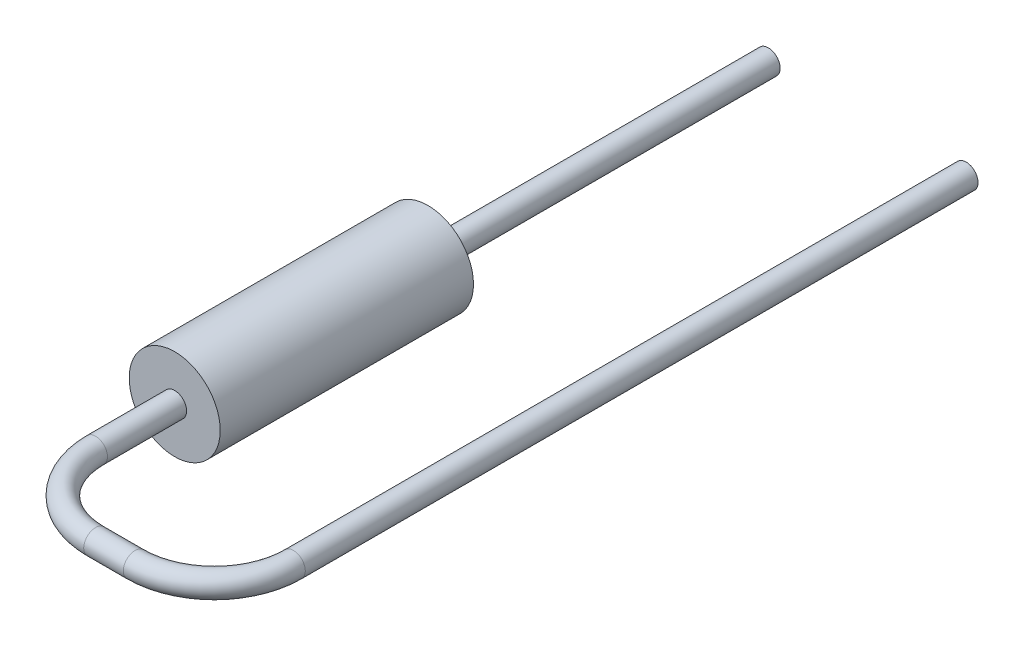
SolidWorks part; units mm, degrees
ref_plane "Front Plane" through (0, 0, 0) normal (0, 0, 1) x (1, 0, 0)
ref_plane "Top Plane" through (0, 0, 0) normal (0, 1, 0) x (1, 0, 0)
ref_plane "Right Plane" through (0, 0, 0) normal (1, 0, 0) x (0, 0, -1)
sketch "Sketch2" plane through (0, 0, 0) normal (0, 0, 1) x (1, 0, 0)
  circle A0 centre (0, 0) radius 1.15
  dimension "D1" = 2.3
extrude "Resistor Body" add sketch "Sketch2" along normal blind 6.4
sketch "Lead1 Path" plane through (0, 0, 0) normal (0, -1, 0) x (1, 0, 0)
  line L2 (0, 6.4) -> (0, 0) construction
  line L3 (0, 6.4) -> (0, 8.4)
  line L4 (5, 8.4) -> (5, -8.6)
  line L5 (2, 10.4) -> (3, 10.4)
  line L6 (1.15, 6.4) -> (-1.15, 6.4) construction
  arc A0 (2, 10.4) -> (0, 8.4) centre (2, 8.4) ccw
  arc A1 (5, 8.4) -> (3, 10.4) centre (3, 8.4) ccw
  point P11 (0, 10.4)
  point P14 (5, 10.4)
  dimension "D4" = 2
  dimension "D1" = 19
  dimension "D2" = 4
  dimension "D3" = 5
sketch "Lead1 Profile" plane through (0, 0, 6.4) normal (0, 0, 1) x (-1, 0, 0)
  circle A0 centre (0, 0) radius 0.3
  dimension "D1" = 0.6
sweep "Lead1" add profiles "Lead1 Profile" path "Lead1 Path"
sketch "Sketch6" plane through (0, 0, 0) normal (0, 0, -1) x (1, 0, 0)
  circle A0 centre (0, 0) radius 0.3 construction
  circle A1 centre (0, 0) radius 0.3
extrude "Lead2" add sketch "Sketch6" along normal up to surface (8.6 mm away) up to face at (4.7, 0, -8.6)
ref_plane "Board Plane" through (0, 0, -5) normal (0, 0, 1) x (1, 0, 0)
sketch "Component_Outline" plane through (0, 0, -5) normal (0, 0, 1) x (1, 0, 0)
  line L0 (5, 0.3) -> (1.1102, 0.3)
  line L3 (5, -0.3) -> (1.1102, -0.3)
  circle A1 centre (0, 0) radius 1.15 construction
  arc A2 (1.1102, 0.3) -> (1.1102, -0.3) centre (0, 0) ccw
  circle A3 centre (5, 0) radius 0.3 construction
  arc A4 (5, -0.3) -> (5, 0.3) centre (5, 0) ccw
